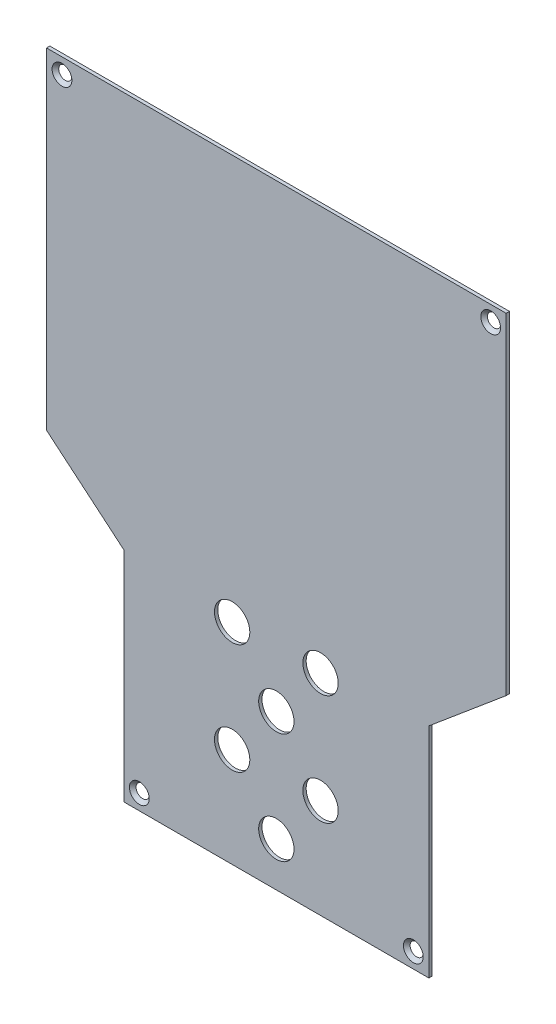
SolidWorks part; units mm, degrees
ref_plane "Plano frontal" through (0, 0, 0) normal (0, 0, 1) x (1, 0, 0)
ref_plane "Plano superior" through (0, 0, 0) normal (0, 1, 0) x (1, 0, 0)
ref_plane "Plano direito" through (0, 0, 0) normal (1, 0, 0) x (0, 0, -1)
sketch "Esboço1" plane through (0, 0, 0) normal (0, 0, 1) x (1, 0, 0)
  line L5 (100.8609, 140.9966) -> (-107.1391, 140.9966)
  line L6 (-107.1391, 140.9966) -> (-107.1391, -8.8424)
  line L7 (-107.1391, -8.8424) -> (-72.1391, -38.2109)
  line L8 (-72.1391, -38.2109) -> (-72.1391, -137.0034)
  line L9 (-72.1391, -137.0034) -> (65.8609, -137.0034)
  line L10 (65.8609, -38.2109) -> (65.8609, -137.0034)
  line L11 (100.8609, -8.8424) -> (65.8609, -38.2109)
  line L12 (100.8609, 140.9966) -> (100.8609, -8.8424)
extrude "Ressalto-extrusão1" add sketch "Esboço1" along normal blind 1.5
sketch "Esboço2" plane through (0, 0, 1.5) normal (0, 0, 1) x (1, 0, 0)
  line L1 (-72.1391, -38.2109) -> (-72.1391, -137.0034) construction
  line L3 (-72.1391, -137.0034) -> (65.8609, -137.0034) construction
  line L4 (-3.1391, -139.8361) -> (-3.1391, -13.3193) construction
  circle A0 centre (-3.1391, -117.0034) radius 8
  circle A1 centre (16.8609, -42.0034) radius 8
  circle A2 centre (-23.1391, -92.0034) radius 8
  circle A3 centre (-3.1391, -67.0034) radius 8
  circle A4 centre (16.8609, -92.0034) radius 8
  circle A5 centre (-23.1391, -42.0034) radius 8
  point P12 (-3.1391, -137.0034)
  dimension "D1" = 69
  dimension "D2" = 20
  dimension "D3" = 20
  dimension "D4" = 25
  dimension "D5" = 25
  dimension "D6" = 20
  dimension "D7" = 25
extrude "Corte-extrusão1" cut sketch "Esboço2" against normal through all
sketch "Esboço3" plane through (0, 0, 1.5) normal (0, 0, 1) x (1, 0, 0)
  line L0 (-3.1391, -154.519) -> (-3.1391, 188.7822) construction
  line L1 (100.8609, 140.9966) -> (-107.1391, 140.9966) construction
  line L3 (-107.1391, 140.9966) -> (-107.1391, -8.8424) construction
  line L4 (-72.1391, -38.2109) -> (-72.1391, -137.0034) construction
  line L5 (-72.1391, -137.0034) -> (65.8609, -137.0034) construction
  circle A0 centre (-100.1391, 133.9966) radius 2
  circle A1 centre (-65.1391, -130.0034) radius 2
  circle A2 centre (58.8609, -130.0034) radius 2
  circle A3 centre (93.8609, 133.9966) radius 2
  dimension "D1" = 7
  dimension "D2" = 7
  dimension "D3" = 7
  dimension "D4" = 7
hole_wizard "Escareado para parafuso Allen sextavado escareado de M41" positions "3DSketch1" profile "Esboço4" countersink size "M4" standard "ISO" end condition through all
sketch3d "3DSketch1"
  point P0 (-100.1391, 133.9966, 1.5)
  point P3 (93.8609, 133.9966, 1.5)
  point P6 (58.8609, -130.0034, 1.5)
  point P9 (-65.1391, -130.0034, 1.5)
sketch "Esboço4" plane through (-100.1391, 133.9966, 1.5) normal (1, 0, 0) x (0, -1, 0)
  line L0 (0, 0) -> (0, 1.5)
  line L1 (0, 1.5) -> (2.25, 1.5)
  line L2 (2.25, 1.5) -> (2.25, 2.23)
  line L3 (2.25, 2.23) -> (4.48, 0)
  line L5 (4.48, 0) -> (0, 0)
  line L6 (-2.25, 2.23) -> (-4.48, 0) construction
  line L11 (0, -6.35) -> (0, 107.95) construction
  dimension "Thru Hole Dia." = 4.5
  dimension "Thru Hole Depth" = 1.5
  dimension "Near C'Sink Dia." = 8.96
  dimension "Near C'Sink Angle" = 90
